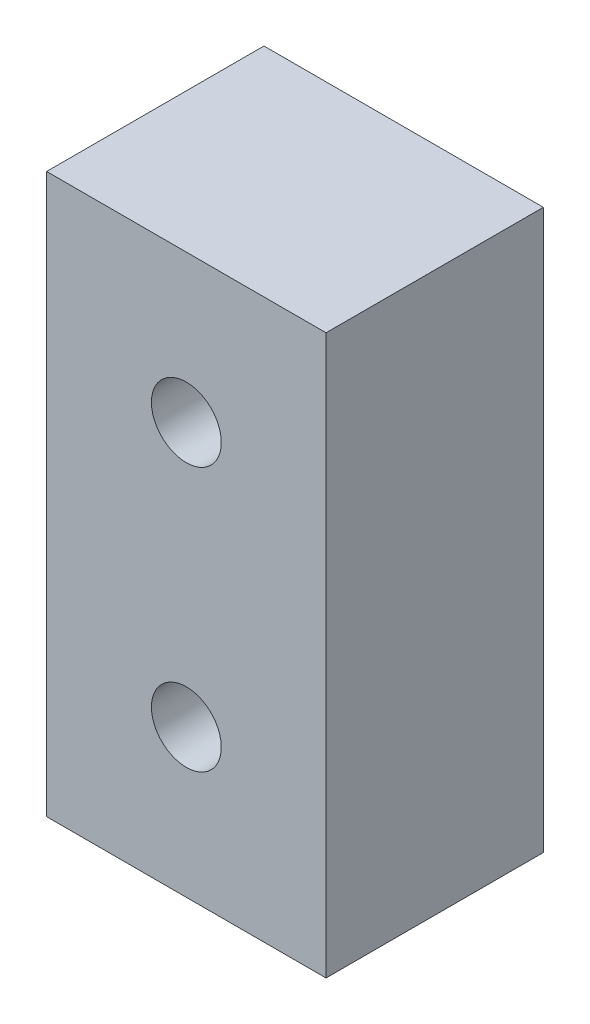
SolidWorks part; units mm, degrees
material "NBR Compact (Nitrile)"
ref_plane "Face" through (0, 0, 0) normal (0, 0, 1) x (1, 0, 0)
ref_plane "Dessus" through (0, 0, 0) normal (0, 1, 0) x (1, 0, 0)
ref_plane "Droite" through (0, 0, 0) normal (1, 0, 0) x (0, 0, -1)
sketch "Esquisse1" plane through (0, 0, 0) normal (0, 0, 1) x (1, 0, 0)
  line L1 (9, -18) -> (-9, -18)
  line L2 (9, -18) -> (9, 18)
  line L3 (9, 18) -> (-9, 18)
  line L4 (-9, -18) -> (-9, 18)
  line L5 (9, -18) -> (-9, 18) construction
  line L6 (9, 18) -> (-9, -18) construction
  point P0 (0, 0)
  dimension "D1" = 18
  dimension "D2" = 36
extrude "Boss.-Extru.1" add sketch "Esquisse1" along normal mid plane 14
hole_wizard "Chambrage pour vis à tête hexagonale M41" positions "Esquisse3" profile "Esquisse2" counterbore size "M4" standard "ISO" end condition through all
sketch "Esquisse3" plane through (0, 0, -7) normal (0, 0, -1) x (-1, 0, 0)
  line L0 (0, 8.5) -> (0, -8.5) construction
  point P0 (0, 8.5)
  point P2 (0, -8.5)
  dimension "D1" = 17
sketch "Esquisse2" plane through (0, 8.5, -7) normal (1, 0, 0) x (0, 1, 0)
  line L0 (0, 0) -> (0, 14)
  line L1 (0, 14) -> (2.25, 14)
  line L3 (2.25, 14) -> (2.25, 4.4)
  line L4 (2.25, 4.4) -> (4, 4.4)
  line L5 (4, 4.4) -> (4, 0)
  line L7 (4, 0) -> (0, 0)
  line L11 (0, -6.35) -> (0, 107.95) construction
  dimension "Diamètre du perçage jusqu'au prochain" = 4.5
  dimension "Profondeur du perçage jusqu'au prochain" = 14
  dimension "Diamètre du chambrage" = 8
  dimension "Profondeur du chambrage" = 4.4
